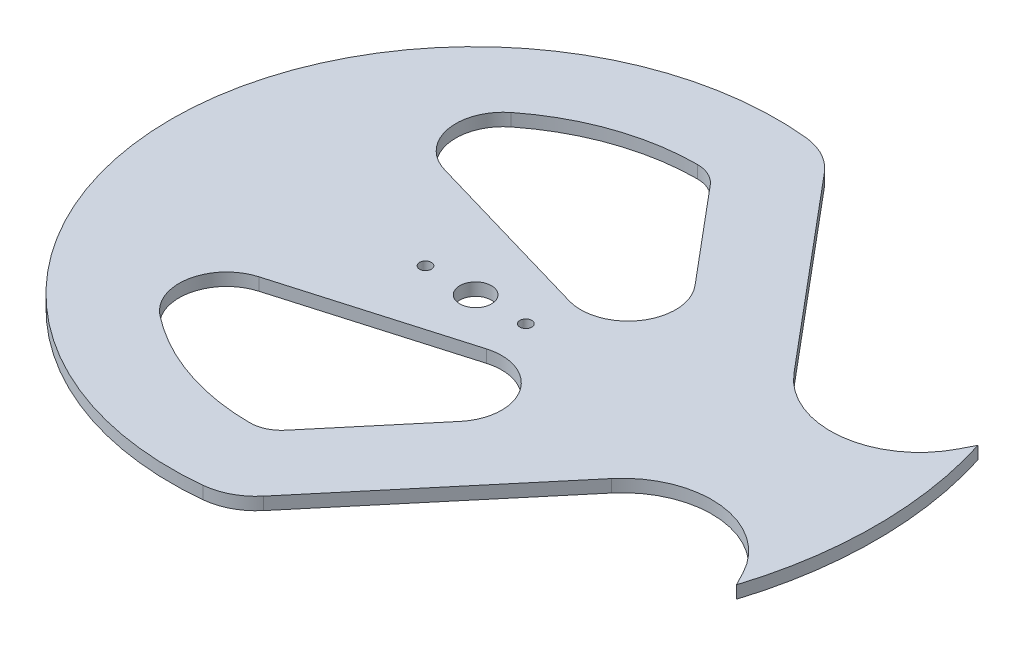
SolidWorks part; units mm, degrees
material "Plain Carbon Steel"
ref_plane "Front Plane" through (0, 0, 0) normal (0, 0, 1) x (1, 0, 0)
ref_plane "Top Plane" through (0, 0, 0) normal (0, 1, 0) x (1, 0, 0)
ref_plane "Right Plane" through (0, 0, 0) normal (1, 0, 0) x (0, 0, -1)
other "Center of Mass"
sketch "Sketch1" plane through (0, 0, 0) normal (0, 1, 0) x (1, 0, 0)
  line L0 (76.6, 0) -> (101.6, 0) construction
  line L1 (0, 0) -> (96.8976, 30.5517) construction
  line L2 (96.8976, 30.5517) -> (96.8976, -30.5517) construction
  line L3 (96.8976, -30.5517) -> (0, 0) construction
  line L4 (96.8976, 30.5517) -> (95.1209, 27.1387)
  line L5 (96.8976, 30.5517) -> (108.753, -7.0488) construction
  line L6 (91.7079, 28.9154) -> (98.5339, 25.362) construction
  line L8 (17.6689, 70.9312) -> (57.8411, 23.0559)
  line L9 (-1000, 0) -> (49000, 0) construction
  line L10 (-1006.8595, 15) -> (48993.1405, 15) construction
  line L11 (17.6689, -70.9312) -> (57.8411, -23.0559)
  line L12 (96.8976, -30.5517) -> (95.1209, -27.1387)
  line L13 (-1060.9264, 23) -> (48939.0736, 23) construction
  line L14 (5.9841, 53.7421) -> (26.1466, 29.7135)
  line L15 (-29.3635, 48.3875) -> (-39.7393, 65.4855) construction
  line L16 (20.6793, 36.2291) -> (36.0002, 49.0848) construction
  line L17 (13.5958, 10.4795) -> (-31.0016, 23.4795)
  line L18 (5.9841, -53.7421) -> (26.1466, -29.7135)
  line L19 (13.5958, -10.4795) -> (-31.0016, -23.4795)
  circle A0 centre (0, 0) radius 101.6 construction
  circle A1 centre (0, 0) radius 76.6 construction
  arc A2 (7.6827, 76.2138) -> (7.6827, -76.2138) centre (0, 0) ccw
  arc A3 (7.6827, 76.2138) -> (17.6689, 70.9312) centre (6.1782, 61.2894) cw
  arc A4 (95.1209, 27.1387) -> (57.8411, 23.0559) centre (75.117, 37.5521) cw
  arc A5 (96.8976, 30.5517) -> (96.8976, -30.5517) centre (0, 0) cw
  arc A6 (7.6827, -76.2138) -> (17.6689, -70.9312) centre (6.1782, -61.2894) ccw
  arc A7 (95.1209, -27.1387) -> (57.8411, -23.0559) centre (75.117, -37.5521) ccw
  arc A8 (-0.168, 56.5998) -> (-35.0811, 44.417) centre (0, 0) ccw
  arc A9 (-0.168, 56.5998) -> (5.9841, 53.7421) centre (-0.1442, 48.5998) cw
  arc A10 (-35.0811, 44.417) -> (-31.0016, 23.4795) centre (-27.6434, 35) ccw
  arc A11 (26.1466, 29.7135) -> (13.5958, 10.4795) centre (16.954, 22) cw
  arc A12 (26.1466, -29.7135) -> (13.5958, -10.4795) centre (16.954, -22) ccw
  arc A13 (-0.168, -56.5998) -> (5.9841, -53.7421) centre (-0.1442, -48.5998) ccw
  arc A14 (-0.168, -56.5998) -> (-35.0811, -44.417) centre (0, 0) cw
  arc A15 (-35.0811, -44.417) -> (-31.0016, -23.4795) centre (-27.6434, -35) cw
  point P0 (75.117, 15)
  point P2 (0, 0)
  point P13 (95.1209, 27.1387)
  point P39 (75.098, 15.095)
  point P47 (98.3538, 25.4772)
  point P48 (108.753, -7.0488)
  dimension "D1" = 203.2
  dimension "D6" = 15
  dimension "D7" = 8
  dimension "D9" = 12
  dimension "D10" = 12
  dimension "D2" = 25
  dimension "D3" = 35
  dimension "D5" = 15
  dimension "D8" = 23
  dimension "D11" = 20
  dimension "D12" = 50
  dimension "D13" = 22
extrude "Boss-Extrude1" add sketch "Sketch1" along normal blind 3.175
sketch "Sketch2" plane through (0, 0, 0) normal (0, 1, 0) x (1, 0, 0)
  line L0 (-201000, 0) -> (249000, 0) construction
  circle A0 centre (0.3786, 0) radius 4
  point P4 (7.0967, 0)
  point P5 (3.2962, 0)
  point P6 (-3.17, 0)
  point P7 (3.1696, 0)
  point P8 (0.3946, 0)
  point P9 (0.3784, 0)
  point P10 (0.3786, 0)
  dimension "D1" = 8
extrude "Cut-Extrude3" cut sketch "Sketch2" along normal through all
sketch "Sketch3" plane through (0, 0, 0) normal (0, 1, 0) x (1, 0, 0)
  line L0 (-12.3214, 0) -> (13.0786, 0) construction
  circle A0 centre (-12.3214, 0) radius 1.5
  circle A1 centre (13.0786, 0) radius 1.5
  circle A2 centre (0.3786, 0) radius 4 construction
  point P6 (0.3786, 0)
  dimension "D1" = 3
  dimension "D2" = 25.4
extrude "Cut-Extrude4" cut sketch "Sketch3" along normal through all
